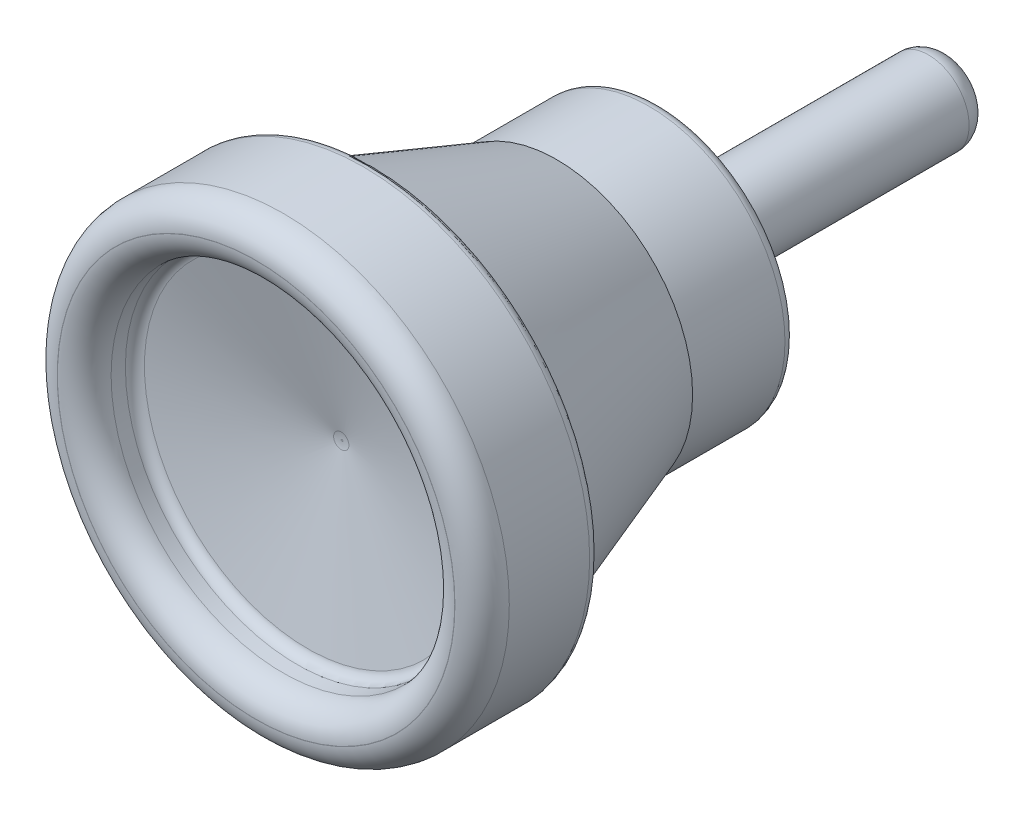
SolidWorks part; units mm, degrees
material "Nikiel"
ref_plane "Płaszczyzna przednia" through (0, 0, 0) normal (0, 0, 1) x (1, 0, 0)
ref_plane "Płaszczyzna górna" through (0, 0, 0) normal (0, 1, 0) x (1, 0, 0)
ref_plane "Płaszczyzna prawa" through (0, 0, 0) normal (1, 0, 0) x (0, 0, -1)
sketch "Szkic1" plane through (0, 0, 0) normal (0, 1, 0) x (1, 0, 0)
  line L0 (0, 4) -> (0, 18.8)
  line L1 (9.25, 0) -> (9.26, 0)
  line L2 (8, 1.25) -> (8, 1.9141)
  line L3 (10.525, 1.265) -> (10.525, 5.0059)
  line L4 (10.268, 5.4429) -> (9.3051, 5.9782)
  line L5 (7.6028, 2.4034) -> (0.3563, 3.9663)
  line L6 (9.0768, 6.248) -> (6.325, 14)
  line L7 (6.325, 14) -> (6.325, 18.3)
  line L8 (0, 18.8) -> (5.825, 18.8)
  line L10 (0, 4) -> (0.0401, 4)
  arc A0 (5.825, 18.8) -> (6.325, 18.3) centre (5.825, 18.3) cw
  arc A1 (10.525, 5.0059) -> (10.268, 5.4429) centre (10.025, 5.0059) ccw
  arc A2 (9.0768, 6.248) -> (9.3051, 5.9782) centre (9.548, 6.4152) ccw
  arc A3 (8, 1.9141) -> (7.6028, 2.4034) centre (7.5, 1.9141) ccw
  arc A4 (9.26, 0) -> (10.525, 1.265) centre (9.26, 1.265) ccw
  arc A5 (8, 1.25) -> (9.25, 0) centre (9.25, 1.25) ccw
  arc A6 (0.0401, 4) -> (0.3563, 3.9663) centre (0.0401, 2.5) cw
revolve "Obrót1" add sketch "Szkic1" angle 360 about L0
sketch "Szkic2" plane through (0, 0, -18.8) normal (0, 0, -1) x (-1, 0, 0)
  circle A0 centre (0, 0) radius 1.9
extrude "Dodanie-wyciągnięcie1" add sketch "Szkic2" along normal blind 13.5
fillet "Zaokrąglenie1" radius 1 1 edges at (-1.9, 0, -32.3)
